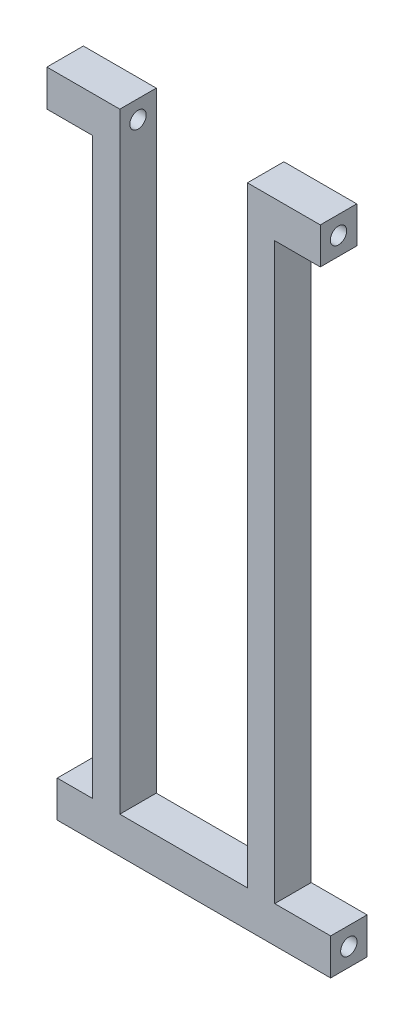
SolidWorks part; units mm, degrees
ref_plane "Alzado" through (0, 0, 0) normal (0, 0, 1) x (1, 0, 0)
ref_plane "Planta" through (0, 0, 0) normal (0, 1, 0) x (1, 0, 0)
ref_plane "Vista lateral" through (0, 0, 0) normal (1, 0, 0) x (0, 0, -1)
sketch "Croquis8" plane through (0, 0, 0) normal (0, 0, 1) x (1, 0, 0)
  line L0 (13.731, 134) -> (13.731, 142)
  line L1 (0, 0) -> (60, 0)
  line L2 (0, 0) -> (0, 8)
  line L3 (0, 8) -> (60, 8)
  line L4 (60, 0) -> (60, 8)
  line L5 (7.731, 8) -> (13.731, 8)
  line L6 (7.731, 8) -> (7.731, 134)
  line L7 (7.731, 134) -> (13.731, 134)
  line L8 (13.731, 8) -> (13.731, 134)
  line L9 (41.731, 8) -> (47.731, 8)
  line L10 (41.731, 8) -> (41.731, 134)
  line L11 (41.731, 134) -> (47.731, 134)
  line L12 (47.731, 8) -> (47.731, 134)
  line L13 (-2.269, 142) -> (57.731, 142)
  line L14 (-2.269, 142) -> (-2.269, 134)
  line L15 (-2.269, 134) -> (57.731, 134)
  line L16 (57.731, 142) -> (57.731, 134)
  line L17 (41.731, 134) -> (41.731, 142)
  dimension "D1" = 8
  dimension "D2" = 60
  dimension "D3" = 6
  dimension "D4" = 6
  dimension "D5" = 10
  dimension "D6" = 10
  dimension "D7" = 60
  dimension "D8" = 28
  dimension "D9" = 8
  dimension "D10" = 134
extrude "Saliente-Extruir1" add sketch "Croquis8" along normal blind 8 contours L14 L15 L7 L0 L13 | L3 L8 L7 L6 | L17 L11 L15 L16 L13 | L3 L12 L11 L10 | L1 L4 L3 L2
hole_wizard "Taladro de margen para M31" positions "Croquis9" profile "Croquis10" hole size "M3" standard "Ansi Metric" end condition through all
sketch "Croquis9" plane through (57.731, 0, 0) normal (1, 0, 0) x (0, 0, -1)
  point P0 (-4, 138)
sketch "Croquis10" plane through (57.731, 138, 4) normal (0, 1, 0) x (0, 0, -1)
  line L0 (0, 0) -> (0, 60)
  line L1 (0, 60) -> (1.8, 60)
  line L2 (1.8, 60) -> (1.8, 0)
  line L5 (1.8, 0) -> (0, 0)
  line L11 (0, -6.35) -> (0, 107.95) construction
  dimension "Diámetro de taladro hasta el siguiente" = 3.6
  dimension "Profundidad de taladro hasta el siguiente" = 60
hole_wizard "Taladro de margen para M32" positions "Croquis11" profile "Croquis12" hole size "M3" standard "Ansi Metric" end condition through all
sketch "Croquis11" plane through (60, 0, 0) normal (1, 0, 0) x (0, 0, -1)
  point P0 (-4, 4)
sketch "Croquis12" plane through (60, 4, 4) normal (0, 1, 0) x (0, 0, -1)
  line L0 (0, 0) -> (0, 62.269)
  line L1 (0, 62.269) -> (1.8, 62.269)
  line L2 (1.8, 62.269) -> (1.8, 0)
  line L5 (1.8, 0) -> (0, 0)
  line L11 (0, -6.35) -> (0, 107.95) construction
  dimension "Diámetro de taladro hasta el siguiente" = 3.6
  dimension "Profundidad de taladro hasta el siguiente" = 62.269
